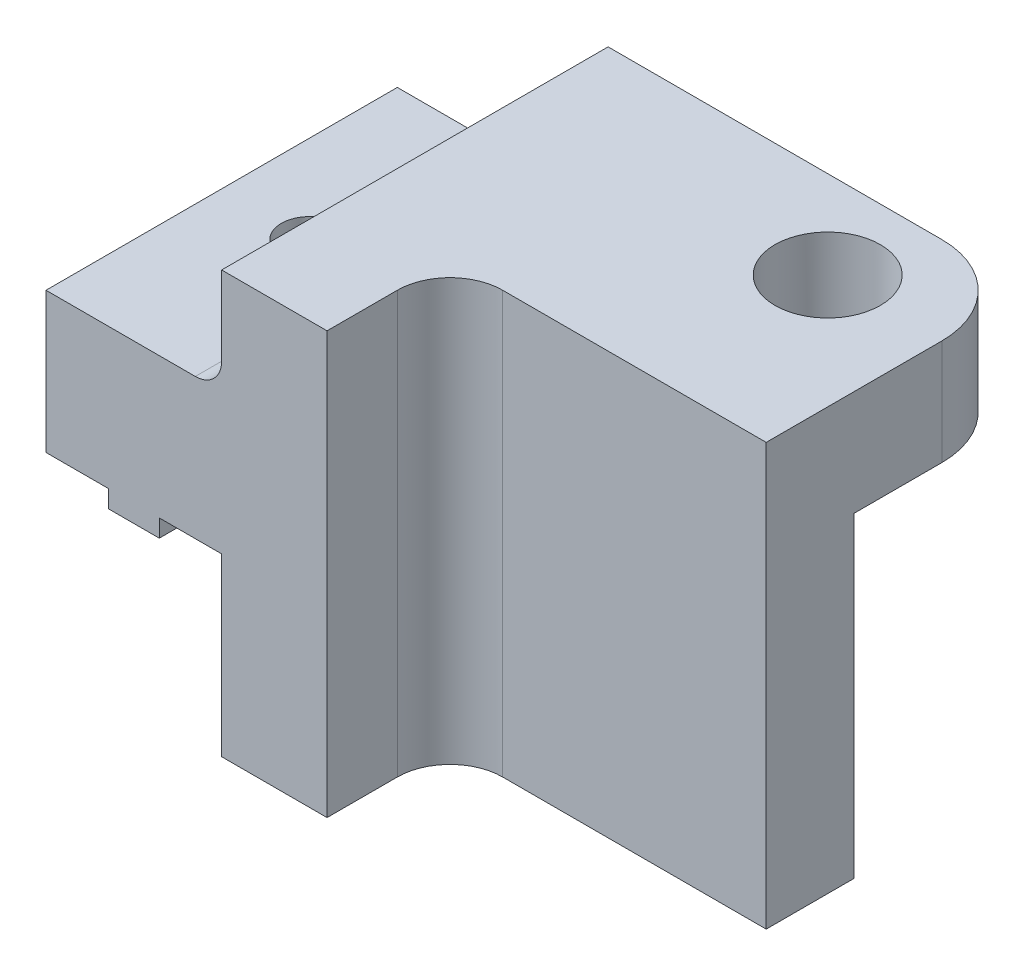
SolidWorks part; units mm, degrees
ref_plane "Front Plane" through (0, 0, 0) normal (0, 0, 1) x (1, 0, 0)
ref_plane "Top Plane" through (0, 0, 0) normal (0, 1, 0) x (1, 0, 0)
ref_plane "Right Plane" through (0, 0, 0) normal (1, 0, 0) x (0, 0, -1)
sketch "Esquisse1" plane through (0, 0, 0) normal (0, 0, 1) x (1, 0, 0)
  line L0 (-12, -12) -> (12, -12)
  line L1 (12, -12) -> (12, -2)
  line L2 (12, -2) -> (15.55, -2)
  line L3 (15.55, -2) -> (15.55, -3)
  line L4 (22, 6) -> (12, 6)
  line L5 (12, 6) -> (12, 12)
  line L6 (12, 12) -> (-12, 12)
  line L7 (-12, 12) -> (-12, -12)
  line L8 (15.55, -3) -> (18.45, -3)
  line L9 (18.45, -3) -> (18.45, -2)
  line L10 (18.45, -2) -> (22, -2)
  line L11 (22, -2) -> (22, 6)
  point P11 (0, -12)
  point P18 (-12, 0)
  dimension "D1" = 2.9
  dimension "D2" = 10
  dimension "D3" = 24
  dimension "D4" = 24
  dimension "D5" = 10
  dimension "D6" = 1
  dimension "D7" = 8
extrude "Main" add sketch "Esquisse1" along normal blind 22
ref_plane "Plan1" through (6, 0, 0) normal (1, 0, 0) x (0, 0, -1)
sketch "Esquisse2" plane through (6, 0, 0) normal (1, 0, 0) x (0, 0, -1)
  line L0 (0, 6) -> (0, 12) construction
  line L1 (-10, 6) -> (0, 6)
  line L2 (-10, 6) -> (-10, -2)
  line L3 (-10, -2) -> (0, -2)
  line L4 (0, 6) -> (0, -2)
  line L5 (-22, 12) -> (0, 12) construction
  line L7 (-22, -12) -> (0, -12) construction
  dimension "D1" = 6
  dimension "D2" = 10
  dimension "D3" = 10
extrude "Enlèv. mat.-Extru.1" cut sketch "Esquisse2" against normal through all
sketch "Esquisse3" plane through (0, 0, 0) normal (0, 0, -1) x (-1, 0, 0)
  line L0 (12, -2) -> (-6, -2) construction
  line L1 (12, -2) -> (-9, -2)
  line L2 (12, -2) -> (12, -12)
  line L3 (12, -12) -> (-9, -12)
  line L4 (-9, -2) -> (-9, -12)
  line L5 (12, -2) -> (12, -12) construction
  line L6 (12, -12) -> (-12, -12) construction
  line L7 (-12, 6) -> (-12, 12) construction
  dimension "D1" = 3
extrude "Enlèv. mat.-Extru.2" cut sketch "Esquisse3" against normal up to surface (10 mm away) up to face at (-3, 2, 10)
sketch "Esquisse4" plane through (0, 12, 0) normal (0, 1, 0) x (1, 0, 0)
  line L0 (12, -22) -> (12, 0) construction
  line L1 (12, 0) -> (-12, 0) construction
  circle A0 centre (-5.5, -5) radius 3
  dimension "D1" = 6
  dimension "D2" = 17.5
  dimension "D3" = 5
extrude "Enlèv. mat.-Extru.3" cut sketch "Esquisse4" against normal through all and the other way through all
fillet "Congé2" radius 5 2 edges at (-12, 9, 0) (6, 6, 5)
sketch "Esquisse6" plane through (-12, 0, 0) normal (-1, 0, 0) x (0, 0, 1)
  line L0 (22, 12) -> (22, -12) construction
  line L1 (22, -12) -> (15, -12)
  line L2 (22, -12) -> (22, 12)
  line L3 (22, 12) -> (15, 12)
  line L4 (15, -12) -> (15, 12)
  line L5 (22, 12) -> (5, 12) construction
  line L6 (10, 6) -> (10, -12) construction
  line L8 (22, -12) -> (10, -12) construction
  dimension "D1" = 5
extrude "Enlèv. mat.-Extru.4" cut sketch "Esquisse6" against normal up to surface (18 mm away)
sketch "Sketch1" plane through (0, 6, 0) normal (0, 1, 0) x (1, 0, 0)
  line L0 (22, -22) -> (22, 0) construction
  line L1 (12, 0) -> (22, 0)
  line L2 (12, 0) -> (12, -2)
  line L3 (12, -2) -> (22, -2)
  line L4 (22, 0) -> (22, -2)
  line L5 (22, -22) -> (12, -22) construction
  dimension "D1" = 20
extrude "Cut-Extrude1" cut sketch "Sketch1" against normal through all
sketch "Sketch2" plane through (0, 6, 0) normal (0, 1, 0) x (1, 0, 0)
  line L0 (22, -22) -> (22, -2) construction
  line L1 (22, -22) -> (12, -22) construction
  circle A0 centre (17, -12) radius 1.6
  dimension "D1" = 3.2
  dimension "D2" = 5
  dimension "D3" = 10
extrude "Cut-Extrude2" cut sketch "Sketch2" against normal through all
fillet "Fillet1" radius 1.5 1 edges at (12, 6, 12)
fillet "Congé3" radius 3 1 edges at (6, 0, 15)
ref_plane "Plan2" through (26, 0, 0) normal (1, 0, 0) x (0, 0, -1)
mirror "Mirror1" about plane through (26, 0, 0) normal (1, 0, 0) of bodies 112
sketch "Sketch3" plane through (26, 0, 0) normal (1, 0, 0) x (0, 0, -1)
  line L1 (0, 12) -> (-22, 12)
  line L2 (0, 12) -> (0, -12)
  line L3 (0, -12) -> (-22, -12)
  line L4 (-22, 12) -> (-22, -12)
extrude "Cut-Extrude3" cut sketch "Sketch3" against normal through all
